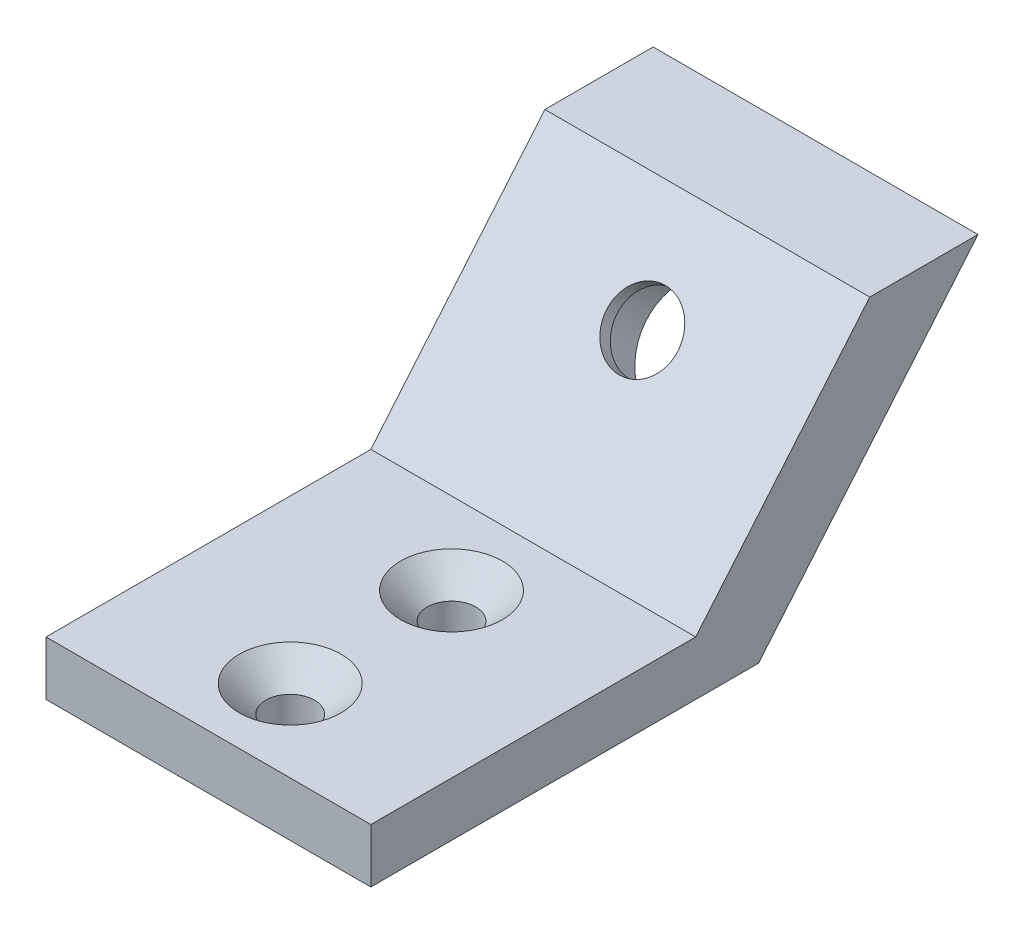
SolidWorks part; units mm, degrees
material "PLA Black"
ref_plane "Front" through (0, 0, 0) normal (0, 0, 1) x (1, 0, 0)
ref_plane "Top" through (0, 0, 0) normal (0, 1, 0) x (1, 0, 0)
ref_plane "Right" through (0, 0, 0) normal (1, 0, 0) x (0, 0, -1)
sketch "Sketch1" plane through (0, 0, 0) normal (0, 0, 1) x (1, 0, 0)
  line L4 (-15, -5) -> (-15, 0)
  line L5 (0, 4.4243) -> (0, -4.5871) construction
  line L6 (-15, -5) -> (15, -5)
  line L10 (15, -5) -> (15, 0)
  line L11 (-15, 0) -> (15, 0)
  dimension "D1" = 5
  dimension "D4" = 30
extrude "Boss-Extrude1" add sketch "Sketch1" along normal blind 30
sketch "Sketch3" plane through (15, 0, 0) normal (1, 0, 0) x (0, 0, -1)
  line L0 (0, 0) -> (16.0697, 19.1511)
  line L1 (16.0697, 19.1511) -> (26.0697, 19.1511)
  line L2 (26.0697, 19.1511) -> (5.8045, -5)
  line L3 (5.8045, -5) -> (0, -5)
  line L5 (0, 0) -> (0, -5)
  dimension "D1" = 50
  dimension "D2" = 10
  dimension "D3" = 25
extrude "Boss-Extrude3" add sketch "Sketch3" against normal up to surface (30 mm away) up to face at (-15, -2.5, 15)
hole_wizard "CBORE for M6 Hex Socket Head Cap Screw1" positions "Sketch5" profile "Sketch6" counterbore size "M6" standard "DIN" end condition through all
sketch "Sketch5" plane through (0, -4.924, -5.8682) normal (0, -0.6428, -0.766) x (-1, 0, 0)
  line L0 (0, 0) -> (0, 35.9415) construction
  line L2 (-17.6898, 15.6644) -> (17.6898, 15.6644) construction
  line L4 (15, 31.4279) -> (-15, 31.4279) construction
  line L5 (15, -0.0992) -> (-15, -0.0992) construction
  point P0 (0, 15.6644)
sketch "Sketch6" plane through (0, 7.0756, -15.9371) normal (1, 0, 0) x (0, 0.766, -0.6428)
  line L0 (0, 0) -> (0, 42.9519)
  line L1 (0, 42.9519) -> (3.3, 42.9519)
  line L3 (3.3, 42.9519) -> (3.3, 6.4)
  line L4 (5.5, 6.4) -> (3.3, 6.4)
  line L5 (5.5, 6.4) -> (5.5, 0.025)
  line L6 (5.5, 0.025) -> (5.525, 0)
  line L7 (5.525, 0) -> (0, 0)
  line L8 (-5.5, 0.025) -> (-5.525, 0) construction
  line L11 (0, -6.35) -> (0, 107.95) construction
  dimension "Thru Hole Dia." = 6.6
  dimension "Thru Hole Depth" = 42.9519
  dimension "C'Bore Dia." = 11
  dimension "C'Bore Depth" = 6.4
  dimension "Near C'Sink Dia." = 11.05
  dimension "Near C'Sink Angle" = 90
hole_wizard "CSK for M4 Countersunk Flat Head Screw1" positions "Sketch8" profile "Sketch7" countersink size "M4" standard "DIN" end condition through all
sketch "Sketch8" plane through (0, 0, 0) normal (0, 1, 0) x (1, 0, 0)
  line L0 (15, -15) -> (-15, -15) construction
  line L1 (15, -30) -> (15, 0) construction
  line L2 (-15, -30) -> (-15, 0) construction
  point P0 (0, -7.55)
  point P2 (0, -22.45)
  dimension "D1" = 14.9
sketch "Sketch7" plane through (0, 0, 7.55) normal (1, 0, 0) x (0, 0, 1)
  line L0 (0, 0) -> (0, 5)
  line L1 (0, 5) -> (2.25, 5)
  line L2 (2.25, 5) -> (2.25, 2.45)
  line L3 (2.25, 2.45) -> (4.7, 0)
  line L5 (4.7, 0) -> (0, 0)
  line L6 (-2.25, 2.45) -> (-4.7, 0) construction
  line L11 (0, -6.35) -> (0, 107.95) construction
  dimension "Thru Hole Dia." = 4.5
  dimension "Thru Hole Depth" = 5
  dimension "Near C'Sink Dia." = 9.4
  dimension "Near C'Sink Angle" = 90
